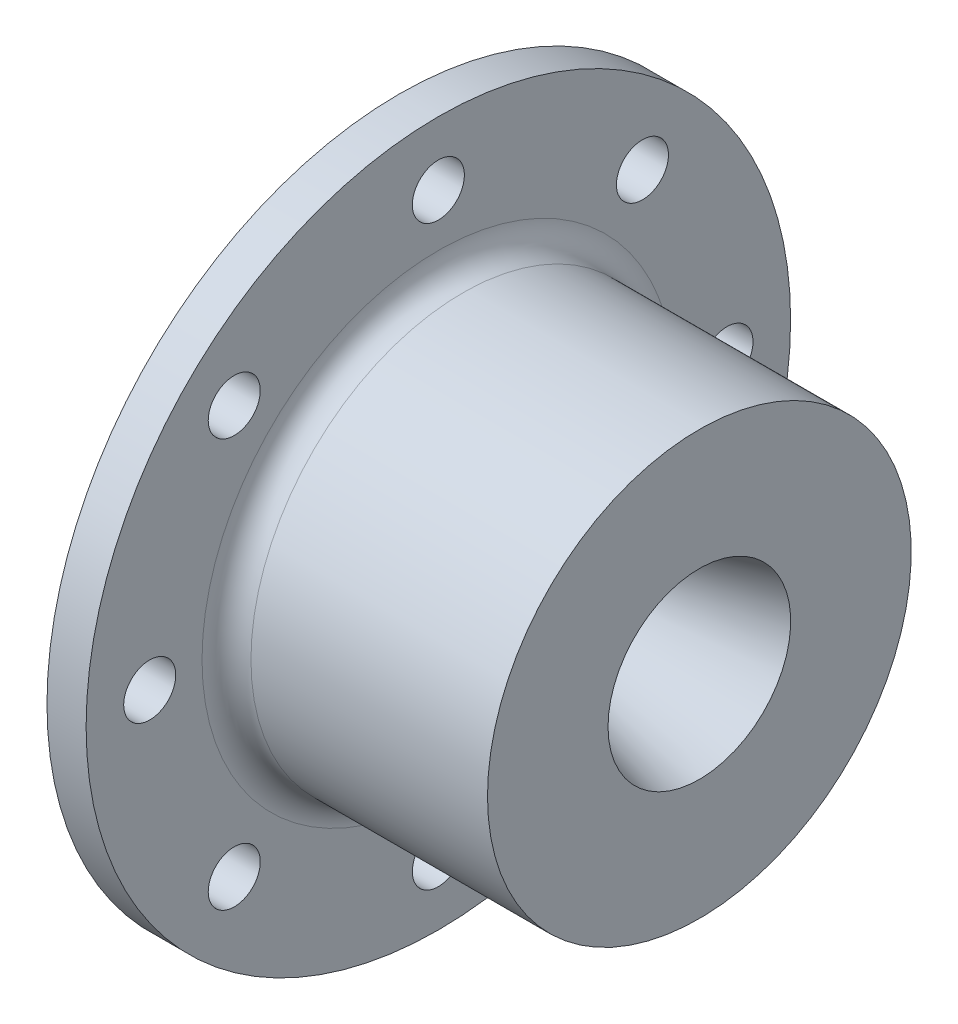
SolidWorks part; units mm, degrees
ref_plane "Front Plane" through (0, 0, 0) normal (0, 0, 1) x (1, 0, 0)
ref_plane "Top Plane" through (0, 0, 0) normal (0, 1, 0) x (1, 0, 0)
ref_plane "Right Plane" through (0, 0, 0) normal (1, 0, 0) x (0, 0, -1)
sketch "Sketch1" plane through (0, 0, 0) normal (0, 0, 1) x (1, 0, 0)
  line L20 (0, 0) -> (32.997, 0) construction
  line L33 (15.2881, 7.1803) -> (21.5111, 7.1803)
  line L34 (15.2881, 7.1803) -> (0, 25.4)
  line L37 (0, 25.4) -> (0, 66.87)
  line L38 (0, 66.87) -> (5.08, 66.87)
  line L39 (5.08, 66.87) -> (5.08, 27.5)
  line L43 (38.9578, 27.5) -> (38.9578, 11.8552)
  line L52 (38.9578, 11.8552) -> (21.5111, 7.1803)
  line L53 (38.9578, 27.5) -> (5.08, 27.5)
  point P1 (2.54, 66.87)
  point P12 (15.2881, 7.1803)
  point P24 (21.5111, 7.1803)
  dimension "D1" = 7.1803
  dimension "D2" = 25.4
  dimension "D5" = 5.08
  dimension "D10" = 15
  dimension "D8" = 11.8552
  dimension "D3" = 27.5
  dimension "D4" = 66.87
  dimension "D6" = 6.223
  dimension "D7" = 50
revolve "Nozzle" add sketch "Sketch1" angle 360 about L20
fillet "Rao outlet radius" radius 2.7429 1 edges at (21.5111, 0, 7.1803)
sketch "Sketch2" plane through (0, 0, 0) normal (-1, 0, 0) x (0, 0, 1)
  point P0 (37.465, 0)
  point P1 (26.4918, -26.4918)
  point P5 (0, -37.465)
  point P6 (-26.4918, -26.4918)
  point P7 (-37.465, 0)
  point P8 (-26.4918, 26.4918)
  point P9 (0, 37.465)
  point P10 (26.4918, 26.4918)
  point P11 (0, 0)
  dimension "D1" = 37.465
  dimension "D2" = 8
hole_wizard "1/4 Clearance Hole1" positions "Sketch2" profile "Sketch3" hole size "1/4" standard "ANSI Inch" end condition through all
sketch "Sketch3" plane through (0, 0, 37.465) normal (0, 1, 0) x (0, 0, 1)
  line L0 (0, 0) -> (0, 38.9578)
  line L1 (0, 38.9578) -> (3.3782, 38.9578)
  line L2 (3.3782, 38.9578) -> (3.3782, 0)
  line L5 (3.3782, 0) -> (0, 0)
  line L11 (0, -6.35) -> (0, 107.95) construction
  dimension "Thru Hole Dia." = 6.7564
  dimension "Thru Hole Depth" = 38.9578
sketch "Sketch5" plane through (0, 0, 0) normal (1, 0, 0) x (0, 0, -1)
  circle A107 centre (0, 0) radius 45.72
  dimension "D1" = 91.44
extrude "Cut-Extrude1" cut sketch "Sketch5" along normal up to surface (5.08 mm away) flip side to cut up to face at (5.08, 0, 40.8432)
fillet "Fillet1" radius 3.175 1 edges at (5.08, 0, 27.5)
fillet "Rao Inlet radius" radius 10.7705 1 edges at (15.2881, 0, 7.1803)
equation "\"radius\"= 1in"
equation "\"Flange\"= 0.55in"
equation "\"Length\"= 2cm"
equation "\"Flange_Thickness\"= 0.2in"
equation "\"offset\"= 0.625cm"
equation "\"D2@Sketch1\"=\"radius\""
equation "\"throat\"= 0.28269in"
equation "\"hole_dia\"= 0.66cm"
equation "\"D1@Sketch1\"=\"throat\""
equation "\"D5@Sketch1\"=\"Flange_Thickness\""
equation "\"Seal_dia\"= 2.5cm"
equation "\"Seal_depth\"= 0.1cm"
equation "\"Seal_width\"= 0.15cm"
equation "\"Nozzle_angle\"= 15"
equation "\"D10@Sketch1\"=\"Nozzle_angle\""
equation "\"nozzle_length\"= 6.34"
equation "\"bolt_head_dia\"=2.3795"
equation "\"bolt_rad\"= \"radius\" + 0.5 * \"Flange\" + 0.2in"
equation "\"scallop_inner_dia\"= 3.3in"
equation "\"exit_rad\"= 1.693cm"
equation "\"D8@Sketch1\"=\"throat\"*(2.726)^0.5"
equation "\"outside_dia\"= 2.75cm"
equation "\"D3@Sketch1\"=\"outside_dia\""
equation "\"D4@Sketch1\"=\"outside_dia\"+\"Flange\"+\"Buffer\""
equation "\"Scallop_OD\"= 0.6in"
equation "\"D3\"= \"Scallop_OD\" / 2"
equation "\"D4\"= \"scallop_inner_dia\" / 2"
equation "\"D1@Sketch2\"=\"bolt_rad\""
equation "\"Buffer\"= 1in"
equation "\"D1@Rao Inlet radius\"=3*\"throat\""
equation "\"D1@Rao outlet radius\"= 0.382 * \"throat\""
equation "\"D1@Rao Inlet radius\"=1.5*\"throat\""
